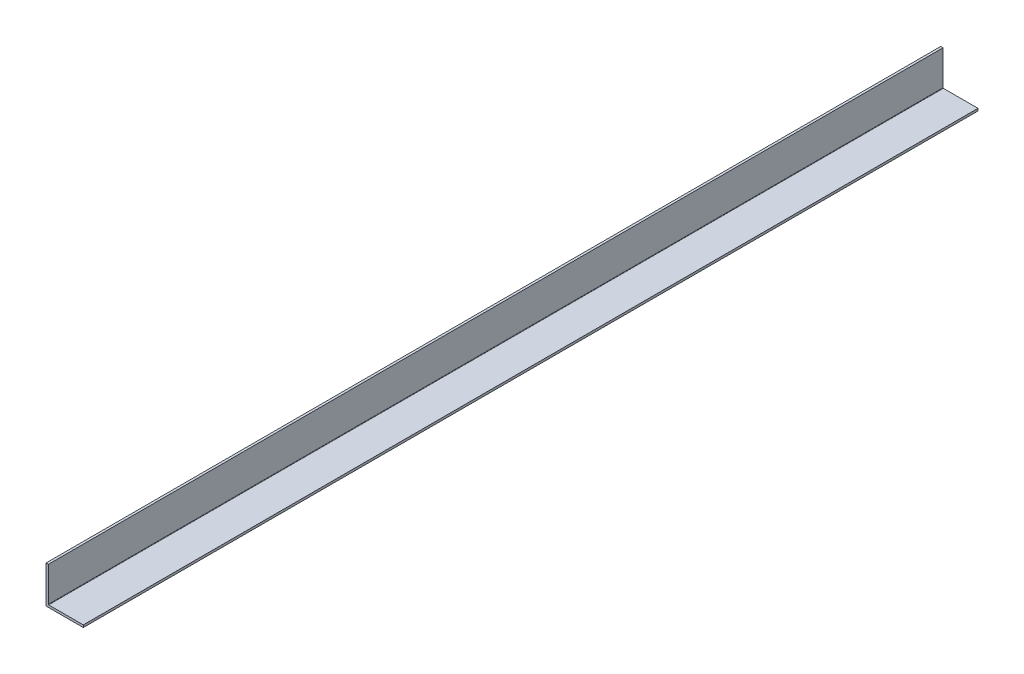
SolidWorks part; units mm, degrees
ref_plane "Front Plane" through (0, 0, 0) normal (0, 0, 1) x (1, 0, 0)
ref_plane "Top Plane" through (0, 0, 0) normal (0, 1, 0) x (1, 0, 0)
ref_plane "Right Plane" through (0, 0, 0) normal (1, 0, 0) x (0, 0, -1)
sketch "Sketch1" plane through (0, 0, 0) normal (0, 0, 1) x (1, 0, 0)
  line L0 (0, 25.4) -> (0, 0) construction
  line L1 (0, 0) -> (25.4, 0) construction
  line L2 (25.4, 0) -> (25.4, 1.5875) construction
  line L3 (25.4, 1.5875) -> (1.5875, 1.5875) construction
  line L4 (1.5875, 1.5875) -> (1.5875, 25.4) construction
  line L6 (1.5875, 25.4) -> (0, 25.4) construction
  arc A0 (1.5875, 1.8415) -> (1.8415, 1.5875) centre (1.8415, 1.8415) ccw construction
  point P4 (0, 0)
  dimension "Inside Corner Radius" = 0.254
  dimension "Outside Height" = 25.4
  dimension "Inside Height" = 23.8125
  dimension "Outside Width" = 25.4
  dimension "Inside Width" = 23.8125
  dimension "Wall Thickness" = 1.5875
  dimension "Shape" = 90
sketch "Sketch2" plane through (0, 0, 0) normal (1, 0, 0) x (0, 0, -1)
  line L0 (304.8, 0) -> (-304.8, 0) construction
  line L1 (-304.8, 25.4) -> (-304.8, 0) construction
  line L2 (304.8, 25.4) -> (304.8, 0) construction
  point P0 (-275.59, 0)
  point P4 (0, 0)
  point P6 (275.59, 0)
  dimension "D1" = 29.21
  dimension "D2" = 29.21
  dimension "D3" = 25.4
  dimension "Length" = 609.6
sketch "Sketch3" plane through (0, 0, 0) normal (0, 0, 1) x (1, 0, 0)
  line L0 (1.5875, 25.4) -> (0, 25.4)
  line L1 (0, 25.4) -> (0, 0)
  line L2 (0, 0) -> (25.4, 0)
  line L3 (25.4, 0) -> (25.4, 1.5875)
  line L4 (25.4, 1.5875) -> (1.5875, 1.5875)
  line L5 (1.5875, 1.5875) -> (1.5875, 25.4)
extrude "Boss-Extrude1" add sketch "Sketch3" along normal mid plane 609.6
fillet "Fillet1" radius 0.254 1 edges at (1.5875, 1.5875, 0)
equation "\"D1@Boss-Extrude1\"=\"Length@Sketch2\""
equation "\"D1@Sketch2\" = \"Outside Width@Sketch1\" * 1.15"
equation "\"D2@Sketch2\"=\"D1@Sketch2\""
equation "\"D1@Fillet1\"=\"Inside Corner Radius@Sketch1\""
equation "\"D3@Sketch2\"=\"Outside Height@Sketch1\""
